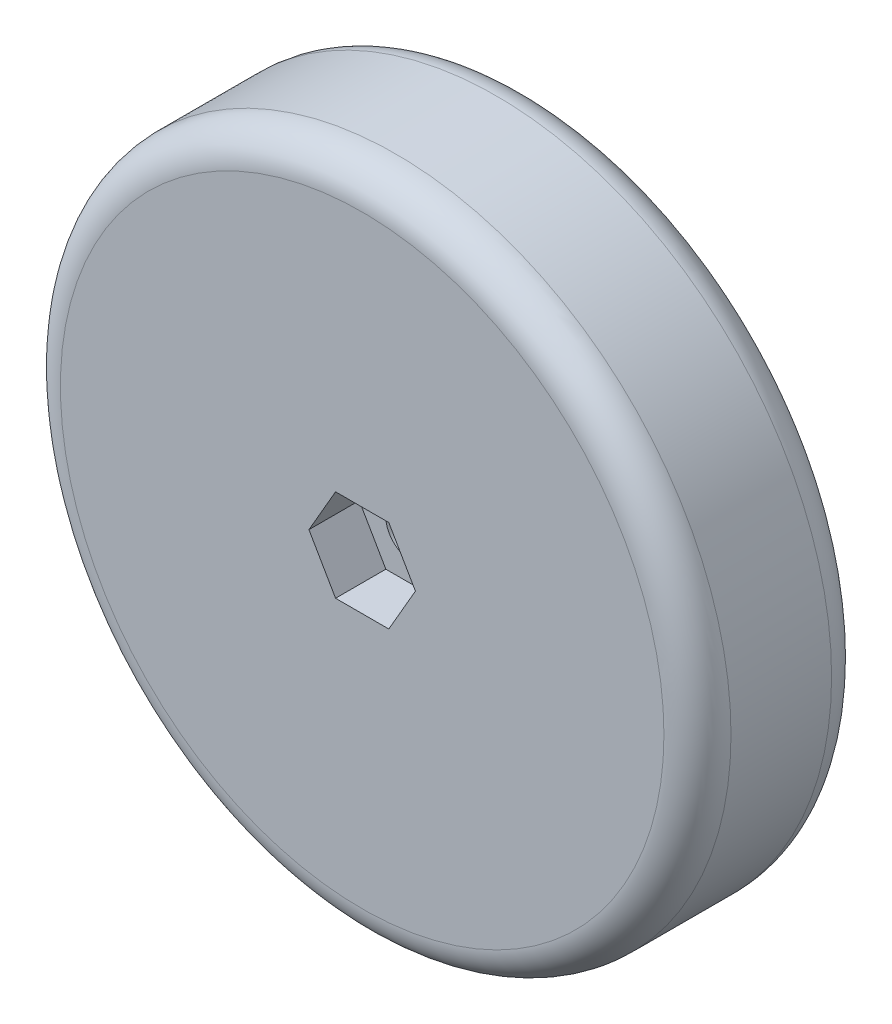
SolidWorks part; units mm, degrees
ref_plane "Piano frontale" through (0, 0, 0) normal (0, 0, 1) x (1, 0, 0)
ref_plane "Piano superiore" through (0, 0, 0) normal (0, 1, 0) x (1, 0, 0)
ref_plane "Piano destro" through (0, 0, 0) normal (1, 0, 0) x (0, 0, -1)
sketch "Schizzo1" plane through (0, 0, 0) normal (0, 0, 1) x (1, 0, 0)
  circle A0 centre (0, 0) radius 20
  circle A1 centre (0, 0) radius 1.6
  dimension "D1" = 40
  dimension "D2" = 3.2
extrude "Estrusione-Estrusione1" add sketch "Schizzo1" along normal blind 10
sketch "Schizzo2" plane through (0, 0, 10) normal (0, 0, 1) x (1, 0, 0)
  line L1 (3.1754, 0) -> (1.5877, 2.75)
  line L2 (1.5877, 2.75) -> (-1.5877, 2.75)
  line L3 (-1.5877, 2.75) -> (-3.1754, 0)
  line L4 (-3.1754, 0) -> (-1.5877, -2.75)
  line L5 (-1.5877, -2.75) -> (1.5877, -2.75)
  line L6 (1.5877, -2.75) -> (3.1754, 0)
  circle A0 centre (0, 0) radius 2.75 construction
  dimension "D1" = 5.5
extrude "Taglio-Estrusione1" cut sketch "Schizzo2" against normal blind 3
fillet "Raccordo1" radius 2 2 edges at (20, 0, 0) (20, 0, 10)
sketch "Schizzo3" plane through (0, 0, 0) normal (0, 0, -1) x (-1, 0, 0)
  circle A0 centre (0, 0) radius 5
  circle A1 centre (0, 0) radius 1.6
  dimension "D1" = 10
extrude "Estrusione-Estrusione2" add sketch "Schizzo3" along normal blind 0.5
